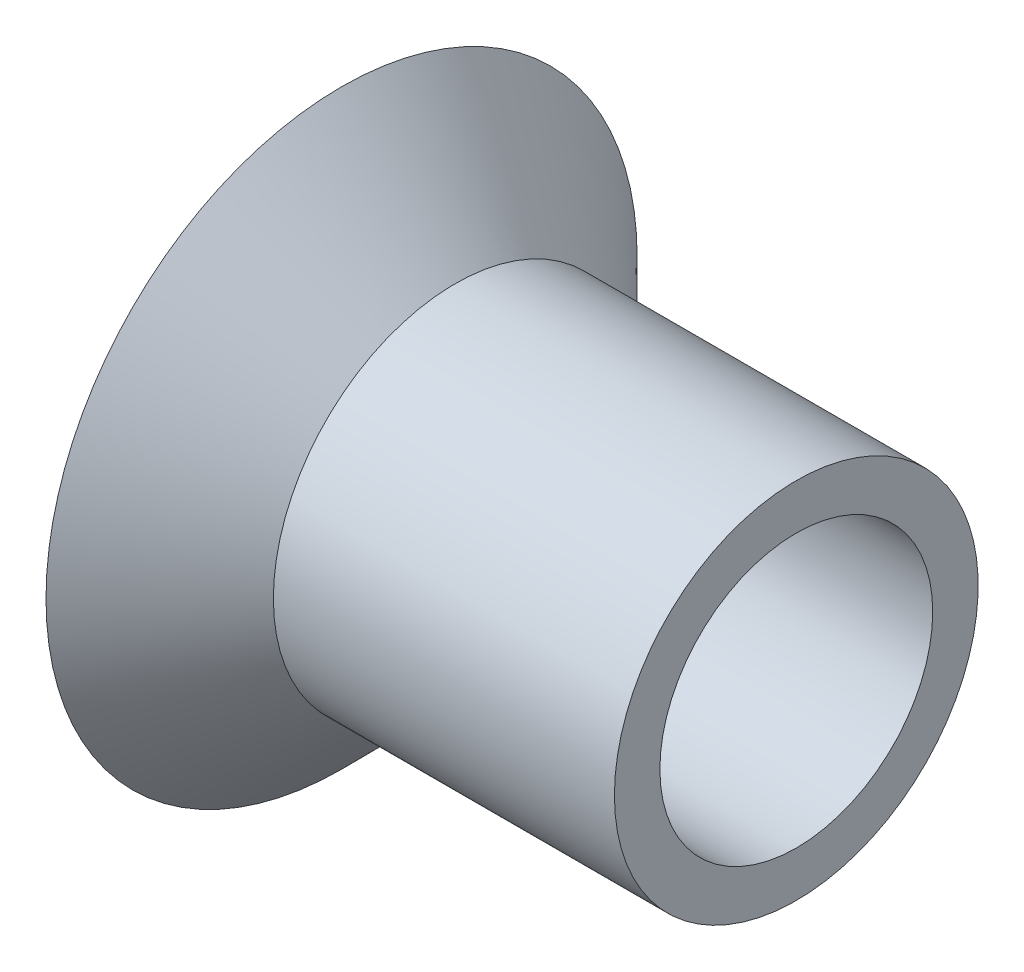
SolidWorks part; units mm, degrees
ref_plane "Front Plane" through (0, 0, 0) normal (0, 0, 1) x (1, 0, 0)
ref_plane "Top Plane" through (0, 0, 0) normal (0, 1, 0) x (1, 0, 0)
ref_plane "Right Plane" through (0, 0, 0) normal (1, 0, 0) x (0, 0, -1)
sketch "Sketch1" plane through (0, 0, 0) normal (0, 0, 1) x (1, 0, 0)
  line L0 (-9.5796, 0) -> (8.3541, 0) construction
  line L1 (-5, -6.5) -> (5, -6.5) construction
  line L2 (-5, -6.5) -> (-5, 6.5) construction
  line L3 (-5, 6.5) -> (5, 6.5) construction
  line L4 (5, -6.5) -> (5, 6.5) construction
  line L5 (-5, -6.5) -> (5, 6.5) construction
  line L6 (-5, 6.5) -> (5, -6.5) construction
  line L7 (5, 0) -> (5, 4) construction
  line L8 (5, 4) -> (-2.5, 4)
  line L9 (-2.5, 4) -> (-5, 6.5)
  line L10 (5, 3) -> (-2.9142, 3)
  line L11 (-2.9142, 3) -> (-5, 5.0858)
  line L12 (-5, 6.5) -> (-5, 5.0858)
  line L13 (5, 4) -> (5, 3)
  line L14 (-2.9142, 3) -> (-5.7071, 5.7929) construction
  point P0 (0, 0)
  dimension "D1" = 10
  dimension "D2" = 13
  dimension "D3" = 4
  dimension "D4" = 45
  dimension "D5" = 1
revolve "Revolve1" add sketch "Sketch1" angle 360 about L0
